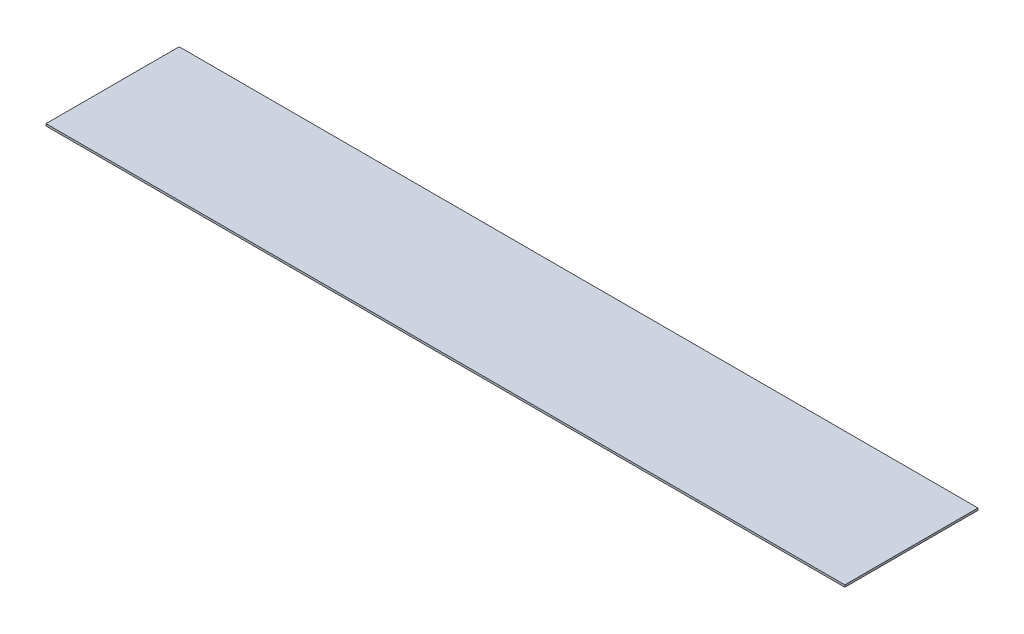
SolidWorks part; units mm, degrees
material "Nylon 101"
ref_plane "Front Plane" through (0, 0, 0) normal (0, 0, 1) x (1, 0, 0)
ref_plane "Top Plane" through (0, 0, 0) normal (0, 1, 0) x (1, 0, 0)
ref_plane "Right Plane" through (0, 0, 0) normal (1, 0, 0) x (0, 0, -1)
sketch "Sketch1" plane through (0, -80.2624, 0) normal (0, -1, 0) x (1, 0, 0)
  line L2 (0, 0) -> (609.6, 0)
  line L3 (0, 0) -> (0, 101.6)
  line L4 (0, 101.6) -> (609.6, 101.6)
  line L5 (609.6, 0) -> (609.6, 101.6)
  dimension "D2" = 609.6
  dimension "D1" = 101.6
extrude "Boss-Extrude1" add sketch "Sketch1" along normal blind 1.5875
